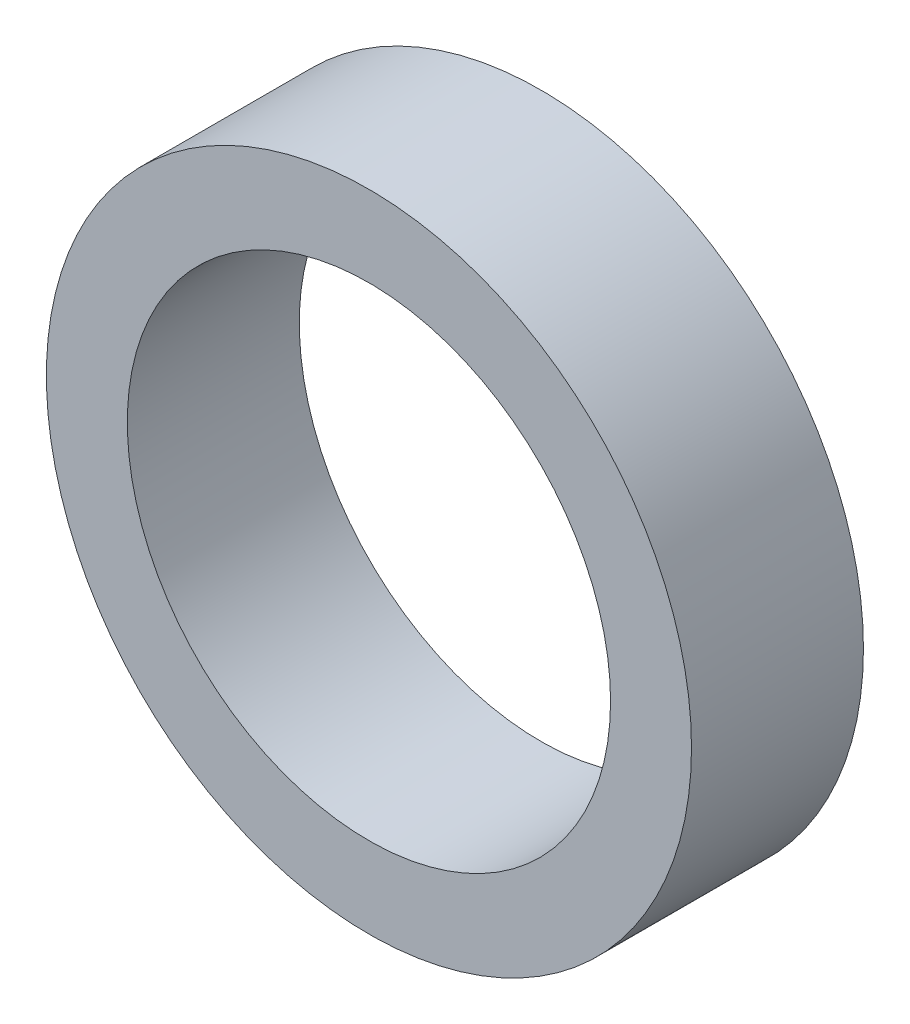
SolidWorks part; units mm, degrees
ref_plane "Ebene vorne" through (0, 0, 0) normal (0, 0, 1) x (1, 0, 0)
ref_plane "Ebene oben" through (0, 0, 0) normal (0, 1, 0) x (1, 0, 0)
ref_plane "Ebene rechts" through (0, 0, 0) normal (1, 0, 0) x (0, 0, -1)
sketch "Skizze1" plane through (0, 0, 0) normal (0, 0, 1) x (1, 0, 0)
  circle A0 centre (0, 0) radius 37.5214
  circle A1 centre (0, 0) radius 28.1055
extrude "Aufsatz-Linear austragen1" add sketch "Skizze1" along normal blind 20
